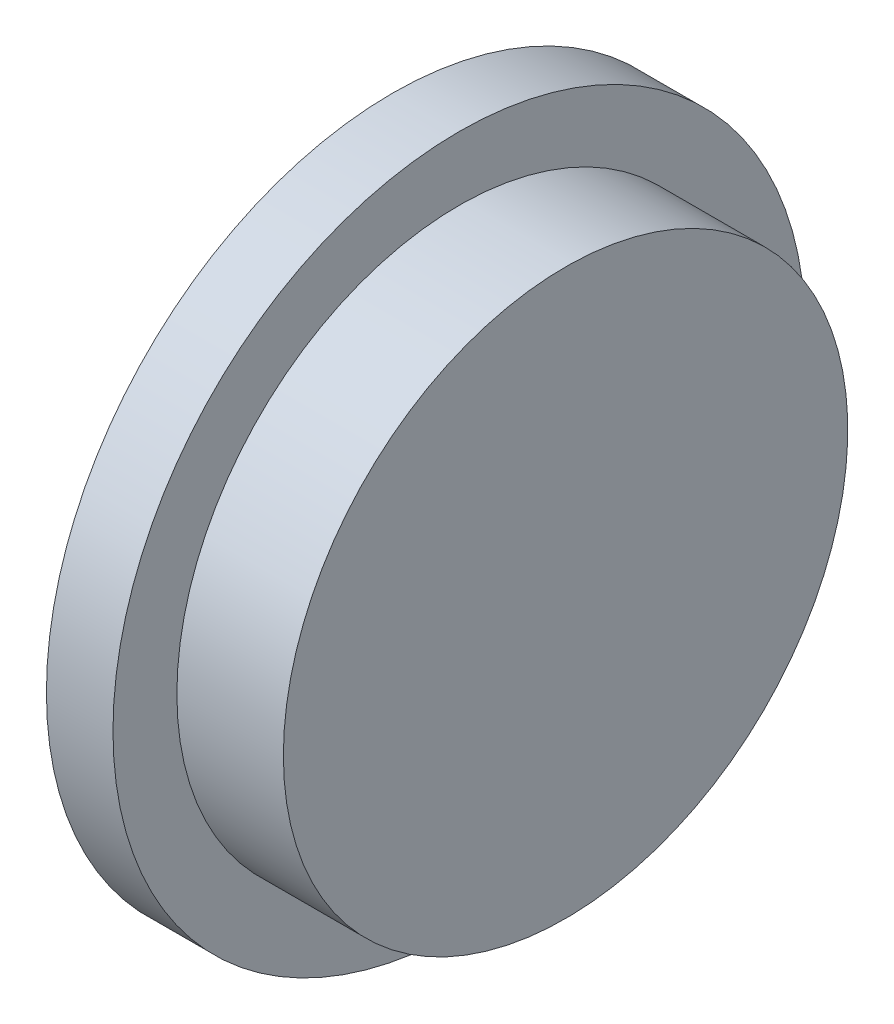
SolidWorks part; units mm, degrees
ref_plane "Přední rovina" through (0, 0, 0) normal (0, 0, 1) x (1, 0, 0)
ref_plane "Vrchní rovina" through (0, 0, 0) normal (0, 1, 0) x (1, 0, 0)
ref_plane "Pravá rovina" through (0, 0, 0) normal (1, 0, 0) x (0, 0, -1)
sketch "Skica1" plane through (0, 0, 0) normal (0, 0, 1) x (1, 0, 0)
  line L0 (0, 0) -> (0, 2.8)
  line L1 (0, 2.8) -> (2, 2.8)
  line L2 (2, 2.8) -> (2, 6.5)
  line L3 (2, 6.5) -> (3.25, 6.5)
  line L4 (3.25, 6.5) -> (3.25, 5.3)
  line L5 (3.25, 5.3) -> (5.25, 5.3)
  line L6 (5.25, 5.3) -> (5.25, 0)
  line L7 (5.25, 0) -> (0, 0)
  line L8 (-1.6714, 0) -> (7.4205, 0) construction
  dimension "D1" = 13
  dimension "D2" = 10.6
  dimension "D3" = 5.6
  dimension "D4" = 2
  dimension "D5" = 2
  dimension "D6" = 5.25
revolve "Rotovat1" add sketch "Skica1" angle 360 about L8
